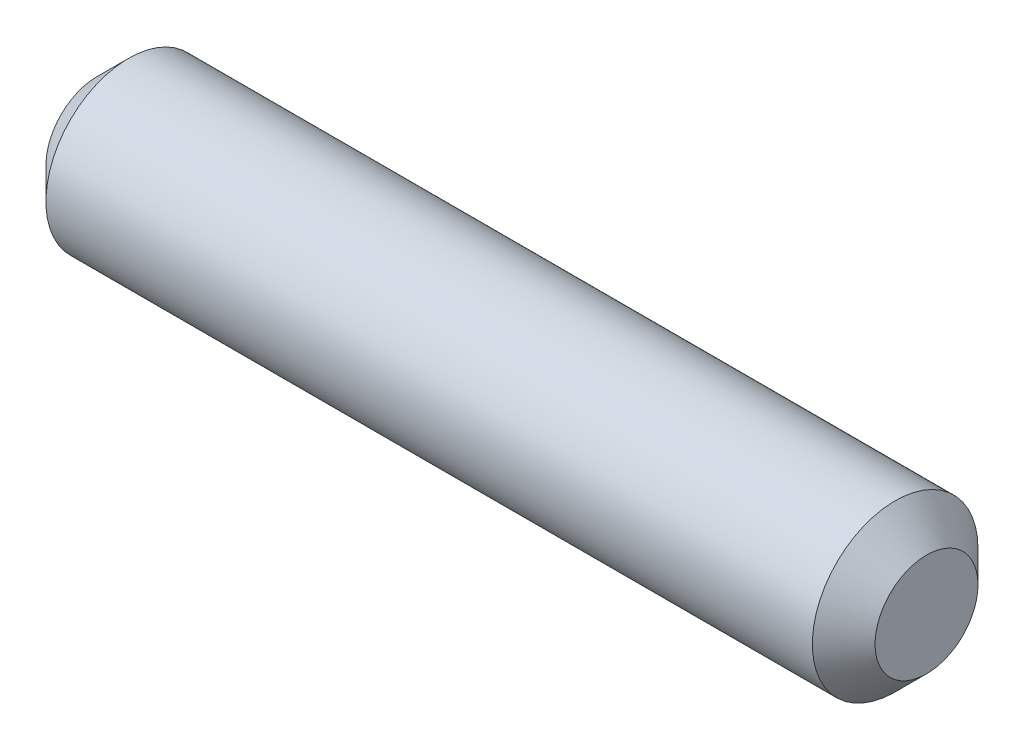
SolidWorks part; units mm, degrees
ref_plane "Plan de face" through (0, 0, 0) normal (0, 0, 1) x (1, 0, 0)
ref_plane "Plan de dessus" through (0, 0, 0) normal (0, 1, 0) x (1, 0, 0)
ref_plane "Plan de droite" through (0, 0, 0) normal (1, 0, 0) x (0, 0, -1)
sketch "Esquisse1" plane through (0, 0, 0) normal (1, 0, 0) x (0, 0, -1)
  circle A0 centre (0, 0) radius 1.585
  dimension "D1" = 3.17
extrude "Boss.-Extru.1" add sketch "Esquisse1" along normal mid plane 15.87
chamfer "Chanfrein1" distance 0.6 angle 45 2 edges at (-7.935, 0, -1.585) (7.935, 0, -1.585)
